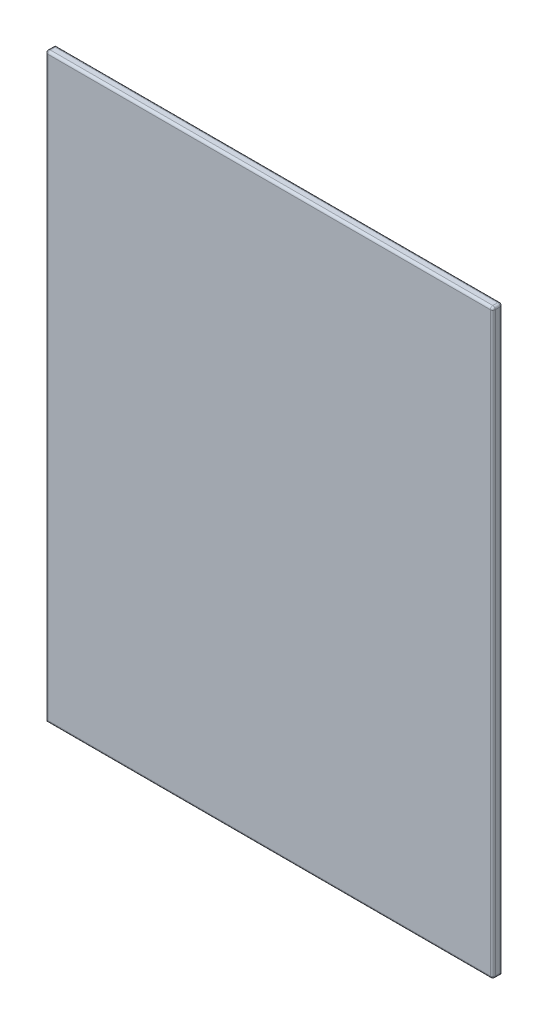
SolidWorks part; units mm, degrees
material "Acrylic (Medium-high impact)"
ref_plane "Front Plane" through (0, 0, 0) normal (0, 0, 1) x (1, 0, 0)
ref_plane "Top Plane" through (0, 0, 0) normal (0, 1, 0) x (1, 0, 0)
ref_plane "Right Plane" through (0, 0, 0) normal (1, 0, 0) x (0, 0, -1)
sketch "Sketch1" plane through (0, 0, 0) normal (0, 0, 1) x (1, 0, 0)
  line L1 (-457.5, 595) -> (457.5, 595)
  line L2 (-457.5, 595) -> (-457.5, -595)
  line L3 (-457.5, -595) -> (457.5, -595)
  line L4 (457.5, 595) -> (457.5, -595)
  line L5 (-457.5, 595) -> (457.5, -595) construction
  line L6 (-457.5, -595) -> (457.5, 595) construction
  point P0 (0, 0)
  dimension "D1" = 915
  dimension "D2" = 1190
extrude "Boss-Extrude1" add sketch "Sketch1" along normal blind 20
fillet "Fillet1" radius 5 9 edges at (457.5, 0, 0) (0, 595, 0) (457.5, 0, 20) (0, 595, 20) (-457.5, 0, 20) (0, -595, 20) (457.5, -595, 10) (-457.5, 595, 10) (457.5, 595, 10)
